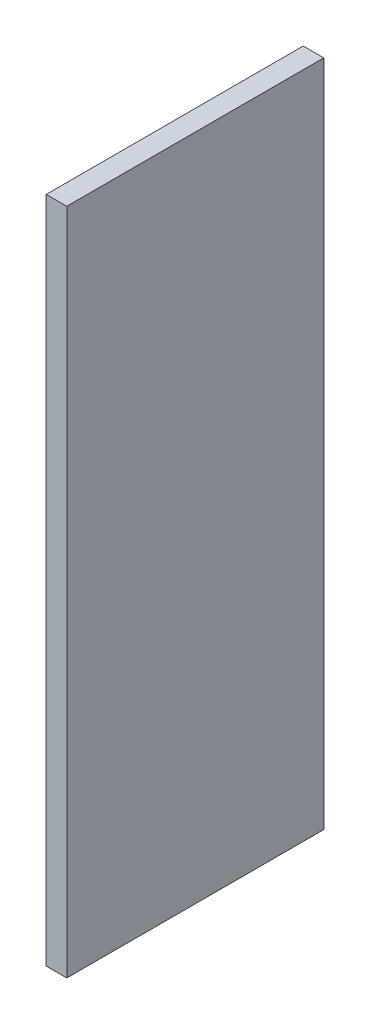
SolidWorks part; units mm, degrees
ref_plane "Front Plane" through (0, 0, 0) normal (0, 0, 1) x (1, 0, 0)
ref_plane "Top Plane" through (0, 0, 0) normal (0, 1, 0) x (1, 0, 0)
ref_plane "Right Plane" through (0, 0, 0) normal (1, 0, 0) x (0, 0, -1)
sketch "Sketch1" plane through (0, 0, 0) normal (0, 0, 1) x (1, 0, 0)
  line L1 (0, 0) -> (0.4, 0)
  line L2 (0, 0) -> (0, 13)
  line L3 (0, 13) -> (0.4, 13)
  line L4 (0.4, 0) -> (0.4, 13)
  dimension "D2" = 13
extrude "Boss-Extrude1" add sketch "Sketch1" along normal blind 5
equation "\"A.L\"= 0.07m"
equation "\"A.h\"= 0.007m"
equation "\"A.d\"= 0.005m"
equation "\"A.delta\"= 45.0001"
equation "\"A.w\"= 0m"
equation "\"A.v\"= 0.013m"
equation "\"A.s\"= 0.014m"
equation "\"A.t\"= 0.007m"
equation "\"B.L\"= 0.065m"
equation "\"B.h\"= 0.008m"
equation "\"B.s\"= 0.016m"
equation "\"B.t\"= 0.008m"
equation "\"C.h\"= 0.0065m"
equation "\"C.d\"= 0.005m"
equation "\"C.L\"= 0.05m"
equation "\"C.wmax\"= 0.003m"
equation "\"D.L\"= 0.06m"
equation "\"D.h\"= 0.008m"
equation "\"D.s\"= 0.012m"
equation "\"D.t\"= 0.008m"
equation "\"a_h\"= 0.0001m"
equation "\"a_d\"= 0.005m"
equation "\"a_L\"= 0.008m"
equation "\"b_h\"= 0.0004m"
equation "\"b_d\"= 0.005m"
equation "\"b_L\"= 0.007m"
equation "\"c_h\"= 0.0001m"
equation "\"c_d\"= 0.005m"
equation "\"c_L\"= 0.01m"
equation "\"d_h\"= 0.0001m"
equation "\"d_d\"= 0.005m"
equation "\"d_L\"= 0.01m"
equation "\"S.h\"= 0.015m"
equation "\"S.L\"= 0.09275m"
equation "\"D1@Sketch1\"=\"b_h\""
equation "\"D2@Sketch1\"=\"b_L\"+0.006"
equation "\"D1@Boss-Extrude1\"=\"b_d\""
